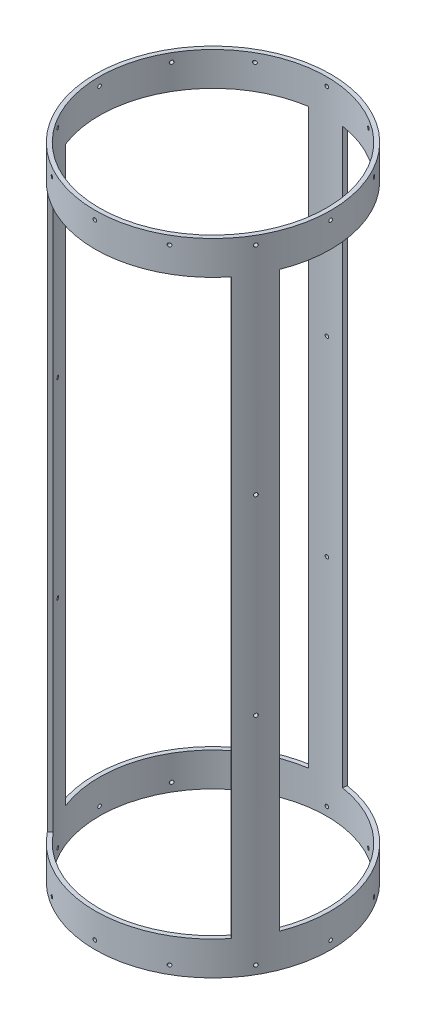
SolidWorks part; units mm, degrees
material "6061-T6 (SS)"
ref_plane "Front Plane" through (0, 0, 0) normal (0, 0, 1) x (1, 0, 0)
ref_plane "Top Plane" through (0, 0, 0) normal (0, 1, 0) x (1, 0, 0)
ref_plane "Right Plane" through (0, 0, 0) normal (1, 0, 0) x (0, 0, -1)
sketch "Sketch1" plane through (0, 0, 0) normal (0, 1, 0) x (1, 0, 0)
  circle A0 centre (0, 0) radius 88.9
  circle A1 centre (0, 0) radius 85.725
  dimension "D1" = 177.8
  dimension "D2" = 171.45
extrude "Boss-Extrude1" add sketch "Sketch1" along normal mid plane 482.854
sketch "Sketch6" plane through (0, -241.427, 0) normal (0, -1, 0) x (-1, 0, 0)
  line L0 (82.7901, -32.3885) -> (79.8333, -31.2317)
  line L1 (13.1222, 87.9262) -> (12.6536, 84.786)
  line L2 (0, 0) -> (0, 85.725) construction
  line L3 (-97.8543, 0) -> (97.8543, 0) construction
  line L4 (0, 0) -> (12.6536, 84.786) construction
  arc A0 (13.1222, 87.9262) -> (82.7901, -32.3885) centre (0, 0) cw
  circle A1 centre (0, 0) radius 88.9 construction
  arc A2 (12.6536, 84.786) -> (79.8333, -31.2317) centre (0, 0) cw
  circle A3 centre (0, 0) radius 85.725 construction
  arc A4 (0, 85.725) -> (12.6536, 84.786) centre (0, 0) cw construction
  dimension "D1" = 153.924
  dimension "D2" = 12.7
extrude "Cut-Extrude5" cut sketch "Sketch6" against normal offset from surface (432.054 mm away) 25.4 from offset 25.4 up to face at (0, 241.427, 88.9) offset against normal yes
pattern_circular "CirPattern5" count 3 over 360 about axis through (0, 0, 0) along (0, 1, 0) of "Cut-Extrude5"
ref_plane "Plane1" through (0, 0, -88.9) normal (0, 0, -1) x (-1, 0, 0)
sketch "Sketch3" plane through (0, 0, 0) normal (0, 0, -1) x (-1, 0, 0)
  line L1 (-88.9, -241.427) -> (88.9, -241.427) construction
  line L3 (-12.8692, 216.027) -> (-12.8692, -216.027) construction
  circle A0 centre (-0.1692, -235.077) radius 1.3525
  dimension "D1" = 6.35
  dimension "D2" = 2.7051
  dimension "D4" = 12.7
extrude "Cut-Extrude2" cut sketch "Sketch3" along normal up to surface (88.8921 mm away)
pattern_circular "CirPattern2" count 12 over 360 about axis through (0, 241.427, 0) along (0, -1, 0) of "Cut-Extrude2"
sketch "Sketch4" plane through (0, 0, -88.9) normal (0, 0, -1) x (-1, 0, 0)
  line L1 (88.9, 241.427) -> (-88.9, 241.427) construction
  circle A0 centre (-0.1692, 235.077) radius 1.3525
  dimension "D1" = 2.7051
  dimension "D2" = 6.35
extrude "Cut-Extrude3" cut sketch "Sketch4" against normal blind 15.24
pattern_circular "CirPattern3" count 12 over 360 about axis through (0, 241.427, 0) along (0, 1, 0) of "Cut-Extrude3"
ref_plane "Plane2" through (0, 0, 88.9) normal (0, 0, 1) x (1, 0, 0)
sketch "Sketch5" plane through (0, 0, 88.9) normal (0, 0, 1) x (1, 0, 0)
  line L0 (-88.9, 216.027) -> (-13.1222, 216.027) construction
  line L1 (88.9, -216.027) -> (13.3458, -216.027) construction
  circle A0 centre (0.1692, 72.009) radius 1.3526
  circle A1 centre (0.1692, -72.009) radius 1.3526
  dimension "D1" = 144.018
  dimension "D2" = 144.018
  dimension "D3" = 2.7051
  dimension "D4" = 2.7051
extrude "Cut-Extrude4" cut sketch "Sketch5" against normal up to surface (177.787 mm away)
pattern_circular "CirPattern4" count 3 over 360 about axis through (0, 241.427, 0) along (0, -1, 0) of "Cut-Extrude4"
